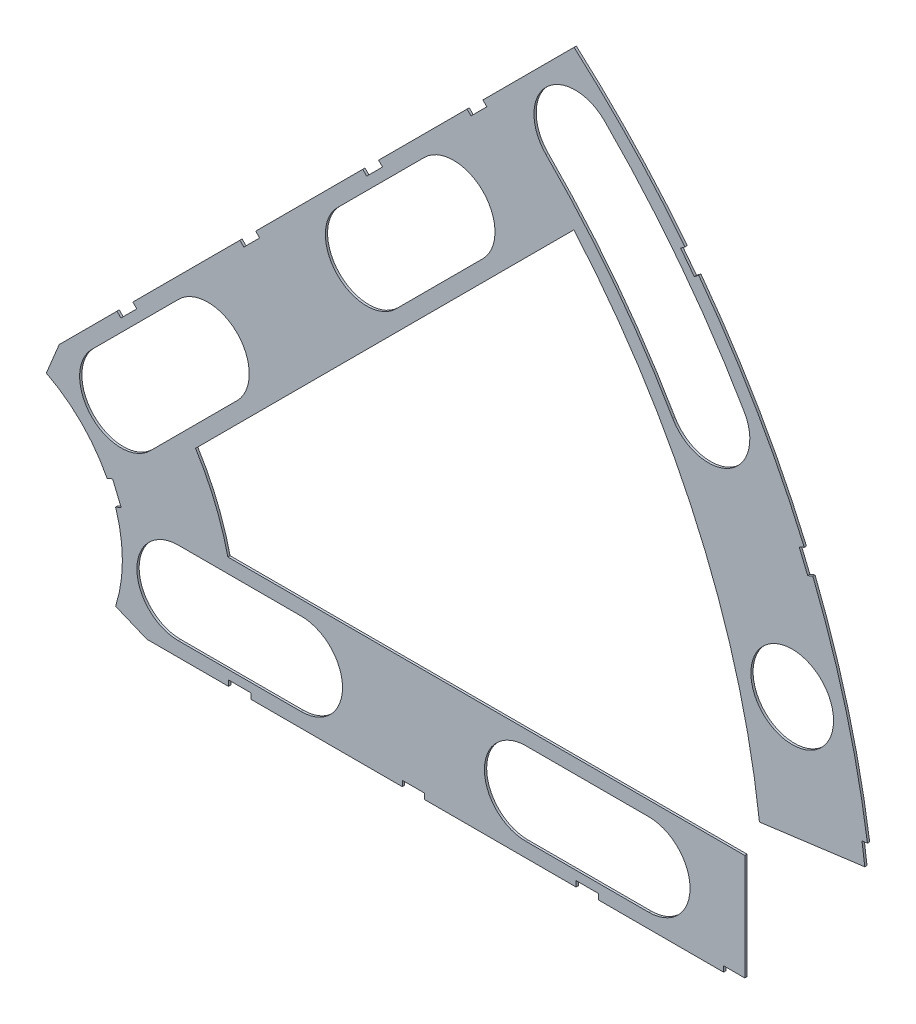
SolidWorks part; units mm, degrees
material "PTFE (general)"
ref_plane "Front Plane" through (0, 0, 0) normal (0, 0, 1) x (1, 0, 0)
ref_plane "Top Plane" through (0, 0, 0) normal (0, 1, 0) x (1, 0, 0)
ref_plane "Right Plane" through (0, 0, 0) normal (1, 0, 0) x (0, 0, -1)
sketch "Sketch1" plane through (0, 0, 0) normal (0, 0, 1) x (1, 0, 0)
  line L0 (0, 0) -> (320.3893, 0) construction
  line L1 (0, 0) -> (155.5285, 155.5285) construction
  line L2 (67.2115, 76.1917) -> (8.6967, 17.6769)
  line L3 (8.6967, 17.6769) -> (7.229, 14.1336)
  line L4 (101.4014, -6.35) -> (18.6489, -6.35)
  line L5 (15.1056, -4.8823) -> (18.6489, -6.35)
  line L6 (88.6729, 6.35) -> (27.8605, 6.35)
  line L9 (67.1914, 58.2111) -> (24.1905, 15.2102)
  line L10 (0, 0) -> (40.4486, 97.6516) construction
  line L11 (0, 0) -> (123.4567, -51.1374) construction
  line L18 (8.6967, 17.6769) -> (13.294, 8.6183) construction
  line L19 (18.6489, -6.35) -> (15.4943, 3.3063) construction
  line L20 (27.8605, 6.35) -> (27.7442, 6.7059) construction
  line L21 (24.1905, 15.2102) -> (24.3599, 14.8764) construction
  arc A0 (7.229, 14.1336) -> (15.1056, -4.8823) centre (0, 0) cw
  arc A1 (67.2115, 76.1917) -> (101.4014, -6.35) centre (0, 0) cw
  arc A2 (24.1905, 15.2102) -> (27.8605, 6.35) centre (0, 0) cw
  arc A3 (67.1914, 58.2111) -> (88.6729, 6.35) centre (0, 0) cw
  arc A8 (13.294, 8.6183) -> (15.4943, 3.3063) centre (0, 0) cw construction
  arc A9 (24.3599, 14.8764) -> (27.7442, 6.7059) centre (0, 0) cw construction
  dimension "D1" = 45
  dimension "D3" = 6.35
  dimension "D4" = 15.875
  dimension "D7" = 22.5
  dimension "D8" = 101.6
  dimension "D11" = 12.7
  dimension "D12" = 12.7
  dimension "D2" = 6.35
  dimension "D5" = 67.5
  dimension "D9" = 1.27
  dimension "D10" = 1.27
  dimension "D6" = 12.7
extrude "Boss-Extrude1" add sketch "Sketch1" along normal blind 0.254
sketch "Sketch2" plane through (0, 0, 0.254) normal (0, 0, 1) x (1, 0, 0)
  line L0 (0, 0) -> (101.6, 0) construction
  line L1 (0, 0) -> (71.842, 71.842) construction
  line L3 (0, 0) -> (22.225, 0) construction
  line L4 (0, 0) -> (15.7154, 15.7154) construction
  line L5 (0, 0) -> (95.25, 0) construction
  line L6 (0, 0) -> (92.0044, 24.6525) construction
  arc A0 (101.4014, -6.35) -> (67.2115, 76.1917) centre (0, 0) ccw construction
  circle A1 centre (22.225, 0) radius 4.699
  arc A2 (15.1056, -4.8823) -> (7.229, 14.1336) centre (0, 0) ccw construction
  circle A3 centre (36.195, 0) radius 4.699
  circle A4 centre (61.722, 0) radius 4.699
  circle A5 centre (75.692, 0) radius 4.699
  circle A6 centre (95.25, 0) radius 4.699
  circle A7 centre (15.7154, 15.7154) radius 4.699
  circle A8 centre (25.5937, 25.5937) radius 4.699
  circle A9 centre (43.644, 43.644) radius 4.699
  circle A10 centre (53.5223, 53.5223) radius 4.699
  circle A11 centre (92.0044, 24.6525) radius 4.699
  circle A12 centre (82.4889, 47.625) radius 4.699
  circle A13 centre (67.3519, 67.3519) radius 4.699
  dimension "D3" = 9.398
  dimension "D1" = 45
  dimension "D2" = 6.35
  dimension "D4" = 6.35
  dimension "D5" = 13.97
  dimension "D7" = 13.97
  dimension "D8" = 19.558
  dimension "D9" = 45
  dimension "D10" = 15
  dimension "D11" = 25.527
  dimension "D6" = 2
extrude "Cut-Extrude1" cut sketch "Sketch2" against normal through all
sketch "Sketch3" plane through (0, 0, 0.254) normal (0, 0, 1) x (1, 0, 0)
  line L0 (15.2664, 24.2467) -> (17.0625, 26.0427)
  line L1 (15.2664, 24.2467) -> (15.7154, 23.7977)
  line L2 (17.0625, 26.0427) -> (17.5115, 25.5937)
  line L3 (15.7154, 23.7977) -> (17.5115, 25.5937)
  line L4 (67.2115, 76.1917) -> (8.6967, 17.6769) construction
  line L5 (44.9911, 53.9713) -> (43.195, 52.1753)
  line L6 (44.9911, 53.9713) -> (45.4401, 53.5223)
  line L7 (43.195, 52.1753) -> (43.644, 51.7263)
  line L8 (45.4401, 53.5223) -> (43.644, 51.7263)
  line L9 (27.94, -6.35) -> (30.48, -6.35)
  line L10 (27.94, -6.35) -> (27.94, -5.715)
  line L11 (30.48, -6.35) -> (30.48, -5.715)
  line L12 (27.94, -5.715) -> (30.48, -5.715)
  line L13 (18.6489, -6.35) -> (101.4014, -6.35) construction
  line L14 (67.437, -6.35) -> (69.977, -6.35)
  line L15 (67.437, -6.35) -> (67.437, -5.715)
  line L16 (69.977, -6.35) -> (69.977, -5.715)
  line L17 (67.437, -5.715) -> (69.977, -5.715)
  line L18 (29.2307, 38.211) -> (31.0268, 40.007)
  line L19 (29.2307, 38.211) -> (29.6797, 37.762)
  line L20 (31.0268, 40.007) -> (31.4758, 39.558)
  line L21 (29.6797, 37.762) -> (31.4758, 39.558)
  line L22 (56.845, 65.8253) -> (55.049, 64.0292)
  line L23 (56.845, 65.8253) -> (57.294, 65.3763)
  line L24 (55.049, 64.0292) -> (55.498, 63.5802)
  line L25 (57.294, 65.3763) -> (55.498, 63.5802)
  line L26 (47.6885, -6.35) -> (50.2285, -6.35)
  line L27 (47.6885, -6.35) -> (47.6885, -5.715)
  line L28 (50.2285, -6.35) -> (50.2285, -5.715)
  line L29 (47.6885, -5.715) -> (50.2285, -5.715)
  line L30 (84.201, -6.35) -> (86.741, -6.35)
  line L31 (84.201, -6.35) -> (84.201, -5.715)
  line L32 (86.741, -6.35) -> (86.741, -5.715)
  line L33 (84.201, -5.715) -> (86.741, -5.715)
  line L34 (0, 0) -> (100.7308, 13.2615) construction
  line L35 (0, 0) -> (93.8662, 38.8806) construction
  line L36 (0, 0) -> (80.6047, 61.8502) construction
  line L37 (0, 0) -> (101.6, 0) construction
  line L38 (99.9355, 14.4377) -> (100.267, 11.9194)
  line L39 (99.9355, 14.4377) -> (101.1946, 14.6035)
  line L40 (100.267, 11.9194) -> (101.5261, 12.0852)
  line L41 (101.1946, 14.6035) -> (101.5261, 12.0852)
  line L42 (99.9355, 14.4377) -> (101.5261, 12.0852) construction
  line L43 (100.267, 11.9194) -> (101.1946, 14.6035) construction
  line L44 (93.7655, 37.4643) -> (94.9388, 37.9503)
  line L45 (93.7655, 37.4643) -> (92.7935, 39.811)
  line L46 (94.9388, 37.9503) -> (93.9668, 40.297)
  line L47 (92.7935, 39.811) -> (93.9668, 40.297)
  line L48 (93.7655, 37.4643) -> (93.9668, 40.297) construction
  line L49 (94.9388, 37.9503) -> (92.7935, 39.811) construction
  line L50 (79.3278, 62.4712) -> (80.874, 60.456)
  line L51 (79.3278, 62.4712) -> (80.3354, 63.2443)
  line L52 (80.874, 60.456) -> (81.8816, 61.2292)
  line L53 (80.3354, 63.2443) -> (81.8816, 61.2292)
  line L54 (79.3278, 62.4712) -> (81.8816, 61.2292) construction
  line L55 (80.874, 60.456) -> (80.3354, 63.2443) construction
  line L56 (13.5939, 7.0054) -> (14.5659, 4.6588)
  line L57 (13.5939, 7.0054) -> (14.7672, 7.4914)
  line L58 (14.5659, 4.6588) -> (15.7393, 5.1448)
  line L59 (14.7672, 7.4914) -> (15.7393, 5.1448)
  line L60 (13.5939, 7.0054) -> (15.7393, 5.1448) construction
  line L61 (14.5659, 4.6588) -> (14.7672, 7.4914) construction
  circle A0 centre (15.7154, 15.7154) radius 4.699 construction
  circle A1 centre (43.644, 43.644) radius 4.699 construction
  circle A2 centre (22.225, 0) radius 4.699 construction
  circle A3 centre (61.722, 0) radius 4.699 construction
  arc A4 (101.4014, -6.35) -> (67.2115, 76.1917) centre (0, 0) ccw construction
  arc A9 (15.1056, -4.8823) -> (7.229, 14.1336) centre (0, 0) ccw construction
  circle A10 centre (25.5937, 25.5937) radius 4.699 construction
  circle A11 centre (53.5223, 53.5223) radius 4.699 construction
  circle A12 centre (36.195, 0) radius 4.699 construction
  circle A13 centre (75.692, 0) radius 4.699 construction
  point P75 (14.6666, 6.0751)
  dimension "D2" = 5.715
  dimension "D3" = 2.54
  dimension "D6" = 5.715
  dimension "D8" = 0.635
  dimension "D9" = 5.715
  dimension "D12" = 5.715
  dimension "D4" = 7.5
  dimension "D5" = 22.5
  dimension "D7" = 37.5
  dimension "D10" = 90
  dimension "D11" = 1.27
  dimension "D14" = 0.635
  dimension "D15" = 90
  dimension "D18" = 0.635
  dimension "D19" = 90
  dimension "D22" = 0.635
  dimension "D20" = 1.27
  dimension "D17" = 0.635
  dimension "D13" = 11.4935
  dimension "D16" = 8.509
  dimension "D21" = 11.4935
  dimension "D23" = 8.509
extrude "Cut-Extrude2" cut sketch "Sketch3" against normal through all
sketch "Sketch5" plane through (0, 0, 0.254) normal (0, 0, 1) x (1, 0, 0)
  line L1 (86.614, -7.62) -> (86.614, 10.2501)
  line L2 (86.614, 10.2501) -> (102.87, 12.3902)
  line L3 (84.201, -5.715) -> (84.201, -6.35) construction
  line L4 (102.87, 12.3902) -> (102.87, -7.62)
  line L5 (102.87, -7.62) -> (86.614, -7.62)
  line L9 (100.5572, 14.5196) -> (99.9355, 14.4377) construction
  line L10 (86.741, -6.35) -> (101.4014, -6.35) construction
  arc A0 (101.4014, -6.35) -> (100.8887, 12.0013) centre (0, 0) ccw construction
  dimension "D1" = 2.413
  dimension "D2" = 2.413
  dimension "D3" = 1.27
  dimension "D4" = 1.27
sketch "Sketch6" plane through (0, 0, 0.254) normal (0, 0, 1) x (1, 0, 0)
  line L0 (0, 0) -> (101.6, 0) construction
  line L1 (0, 0) -> (71.842, 71.842) construction
  line L2 (0, 0) -> (87.9882, 50.8) construction
  line L3 (0, 0) -> (98.1381, 26.296) construction
  line L4 (15.7154, 15.7154) -> (25.5937, 25.5937) construction
  line L5 (12.3928, 19.0381) -> (22.271, 28.9164)
  line L6 (19.0381, 12.3928) -> (28.9164, 22.271)
  line L7 (43.644, 43.644) -> (53.5223, 53.5223) construction
  line L8 (40.3213, 46.9667) -> (50.1996, 56.845)
  line L9 (46.9667, 40.3213) -> (56.845, 50.1996)
  line L10 (22.225, 0) -> (36.195, 0) construction
  line L11 (22.225, 4.699) -> (36.195, 4.699)
  line L12 (22.225, -4.699) -> (36.195, -4.699)
  line L13 (61.722, 0) -> (75.692, 0) construction
  line L14 (61.722, 4.699) -> (75.692, 4.699)
  line L15 (61.722, -4.699) -> (75.692, -4.699)
  arc A0 (79.8253, 62.8529) -> (67.2115, 76.1917) centre (0, 0) ccw construction
  arc A1 (12.3928, 19.0381) -> (19.0381, 12.3928) centre (15.7154, 15.7154) ccw
  arc A2 (28.9164, 22.271) -> (22.271, 28.9164) centre (25.5937, 25.5937) ccw
  arc A3 (40.3213, 46.9667) -> (46.9667, 40.3213) centre (43.644, 43.644) ccw
  arc A4 (56.845, 50.1996) -> (50.1996, 56.845) centre (53.5223, 53.5223) ccw
  arc A5 (101.4014, -6.35) -> (100.8887, 12.0013) centre (0, 0) ccw construction
  arc A6 (22.225, 4.699) -> (22.225, -4.699) centre (22.225, 0) ccw
  arc A7 (93.3728, 40.0509) -> (81.3715, 60.8378) centre (0, 0) ccw construction
  arc A8 (100.5572, 14.5196) -> (94.3448, 37.7043) centre (0, 0) ccw construction
  arc A9 (36.195, -4.699) -> (36.195, 4.699) centre (36.195, 0) ccw
  arc A10 (61.722, 4.699) -> (61.722, -4.699) centre (61.722, 0) ccw
  arc A11 (75.692, -4.699) -> (75.692, 4.699) centre (75.692, 0) ccw
  circle A12 centre (53.5223, 53.5223) radius 4.699 construction
  circle A13 centre (25.5937, 25.5937) radius 4.699 construction
  arc A17 (82.4889, 47.625) -> (67.3519, 67.3519) centre (0, 0) ccw construction
  arc A18 (86.5584, 49.9745) -> (70.6746, 70.6746) centre (0, 0) ccw
  arc A19 (78.4195, 45.2755) -> (64.0292, 64.0292) centre (0, 0) ccw
  arc A20 (78.4195, 45.2755) -> (86.5584, 49.9745) centre (82.4889, 47.625) ccw
  arc A21 (70.6746, 70.6746) -> (64.0292, 64.0292) centre (67.3519, 67.3519) ccw
  point P4 (20.6546, 20.6546)
  point P13 (48.5832, 48.5832)
  point P37 (29.21, 0)
  point P48 (68.707, 0)
  point P68 (75.5669, 57.9845)
  dimension "D2" = 9.398
  dimension "D1" = 45
  dimension "D4" = 9.398
  dimension "D5" = 9.398
extrude "Cut-Extrude4" cut sketch "Sketch6" against normal through all
extrude "Cut-Extrude5" cut sketch "Sketch5" against normal through all
equation "\"cSep\"= 1.005"
equation "\"D11@Sketch2\"=\"cSep\""
equation "\"cSep2\"= \"D8@Sketch2\""
equation "\"D13@Sketch3\"=\"cSep\"/2-.05"
equation "\"D16@Sketch3\"=\"cSep2\"/2-.05"
equation "\"D21@Sketch3\"=\"cSep\"/2-.05"
equation "\"D23@Sketch3\"=\"cSep2\"/2-.05"
